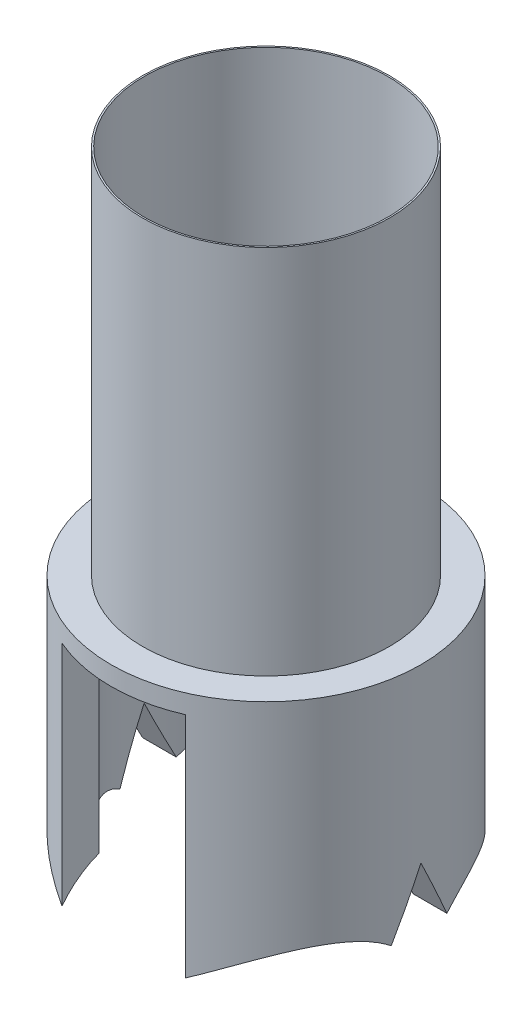
SolidWorks part; units mm, degrees
material "PVC 0.007 Plasticized"
ref_plane "Front Plane" through (0, 0, 0) normal (0, 0, 1) x (1, 0, 0)
ref_plane "Top Plane" through (0, 0, 0) normal (0, 1, 0) x (1, 0, 0)
ref_plane "Right Plane" through (0, 0, 0) normal (1, 0, 0) x (0, 0, -1)
other "Configuration Table"
sketch "Sketch1" plane through (0, 0, 0) normal (0, 1, 0) x (1, 0, 0)
  circle A0 centre (0, 0) radius 1.9939
  dimension "D1" = 3.9878
extrude "Boss-Extrude1" add sketch "Sketch1" along normal blind 5.9944
sketch "Sketch2" plane through (0, 0, 0) normal (0, 1, 0) x (1, 0, 0)
  circle A0 centre (0, 0) radius 2.5019
  dimension "D1" = 5.0038
extrude "Boss-Extrude2" add sketch "Sketch2" against normal blind 3.9878
sketch "Sketch3" plane through (0, 5.9944, 0) normal (0, 1, 0) x (1, 0, 0)
  circle A0 centre (0, 0) radius 1.9685
  dimension "D1" = 3.937
extrude "Cut-Extrude1" cut sketch "Sketch3" against normal through all
ref_plane "Plane1" through (0, 0, 2.5019) normal (0, 0, 1) x (1, 0, 0)
sketch "Sketch4" plane through (0, 0, 2.5019) normal (0, 0, 1) x (1, 0, 0)
  line L0 (-2.5019, -3.9878) -> (2.5019, -3.9878) construction
  line L1 (-1.0033, -3.9878) -> (0.9957, -3.9878)
  line L2 (-1.0033, -3.9878) -> (-1.0033, -0.3048)
  line L3 (-1.0033, -0.3048) -> (0.9957, -0.3048)
  line L4 (0.9957, -3.9878) -> (0.9957, -0.3048)
  line L5 (0, 0) -> (0, -3.9878) construction
  dimension "D1" = 3.683
  dimension "D2" = 1.999
  dimension "D3" = 1.0033
extrude "Cut-Extrude2" cut sketch "Sketch4" against normal through all
ref_plane "Plane2" through (2.5019, 0, 0) normal (1, 0, 0) x (0, 0, -1)
sketch "Sketch5" plane through (2.5019, 0, 0) normal (1, 0, 0) x (0, 0, -1)
  line L1 (0.4634, -3.7311) -> (0, -2.7714)
  line L2 (0, -2.7714) -> (-0.44, -3.7311)
  line L3 (-2.2952, -3.9878) -> (2.2952, -3.9878)
  arc A2 (-2.2952, -3.9878) -> (-0.44, -3.7311) centre (-1.2393, -4.7871) cw
  arc A3 (2.2952, -3.9878) -> (0.4634, -3.7311) centre (1.251, -4.7754) ccw
ref_plane "Plane3" through (-2.5019, 0, 0) normal (1, 0, 0) x (0, 0, -1)
sketch "Sketch6" plane through (-2.5019, 0, 0) normal (1, 0, 0) x (0, 0, -1)
  line L0 (-2.2952, -3.9878) -> (2.2952, -3.9878)
  line L1 (-0.44, -3.7311) -> (0, -2.7714)
  line L2 (0, -2.7714) -> (0.4634, -3.7311)
  arc A0 (2.2952, -3.9878) -> (0.4634, -3.7311) centre (1.251, -4.7754) ccw
  arc A1 (-2.2952, -3.9878) -> (-0.44, -3.7311) centre (-1.2393, -4.7871) cw
extrude "Cut-Extrude3" cut sketch "Sketch6" along normal up to next
extrude "Cut-Extrude4" cut sketch "Sketch5" against normal up to next
